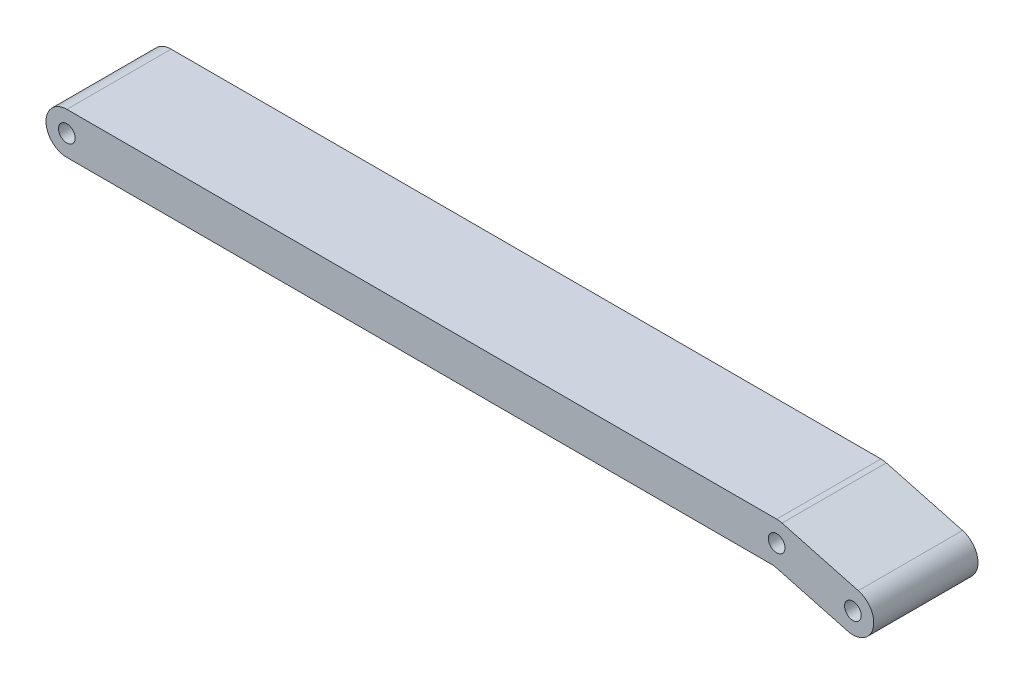
SolidWorks part; units mm, degrees
ref_plane "Front" through (0, 0, 0) normal (0, 0, 1) x (1, 0, 0)
ref_plane "Top" through (0, 0, 0) normal (0, 1, 0) x (1, 0, 0)
ref_plane "Right" through (0, 0, 0) normal (1, 0, 0) x (0, 0, -1)
sketch "Sketch1" plane through (0, 0, 0) normal (0, 0, 1) x (1, 0, 0)
  line L0 (-244.3, 289.2) -> (96.13, 289.2) construction
  line L1 (-244.3, 299.2) -> (96.13, 299.2)
  line L2 (-244.3, 279.2) -> (94.8133, 279.2)
  line L3 (96.13, 289.2) -> (132.7, 279.4) construction
  line L4 (98.7185, 298.8592) -> (135.2885, 289.0592)
  line L5 (94.8133, 279.2) -> (130.1115, 269.7408)
  circle A0 centre (96.13, 289.2) radius 4
  circle A1 centre (132.7, 279.4) radius 4
  circle A2 centre (-244.3, 289.2) radius 4
  arc A3 (-244.3, 299.2) -> (-244.3, 279.2) centre (-244.3, 289.2) ccw
  arc A5 (98.7185, 298.8592) -> (96.13, 299.2) centre (96.13, 289.2) ccw
  arc A6 (130.1115, 269.7408) -> (135.2885, 289.0592) centre (132.7, 279.4) ccw
  arc A7 (98.7185, 298.8592) -> (96.13, 299.2) centre (96.13, 289.2) ccw
  point P7 (-74.085, 289.2)
  point P13 (114.415, 284.3)
  dimension "D6" = 8
  dimension "D1" = 244.3
  dimension "D2" = 96.13
  dimension "D3" = 132.7
  dimension "D4" = 279.4
  dimension "D5" = 289.2
  dimension "D7" = 20
  dimension "D8" = 20
extrude "Boss-Extrude1" add sketch "Sketch1" along normal blind 50 contours L5 A6 L4 A5 L1 A3 L2 A0 A1 A2
